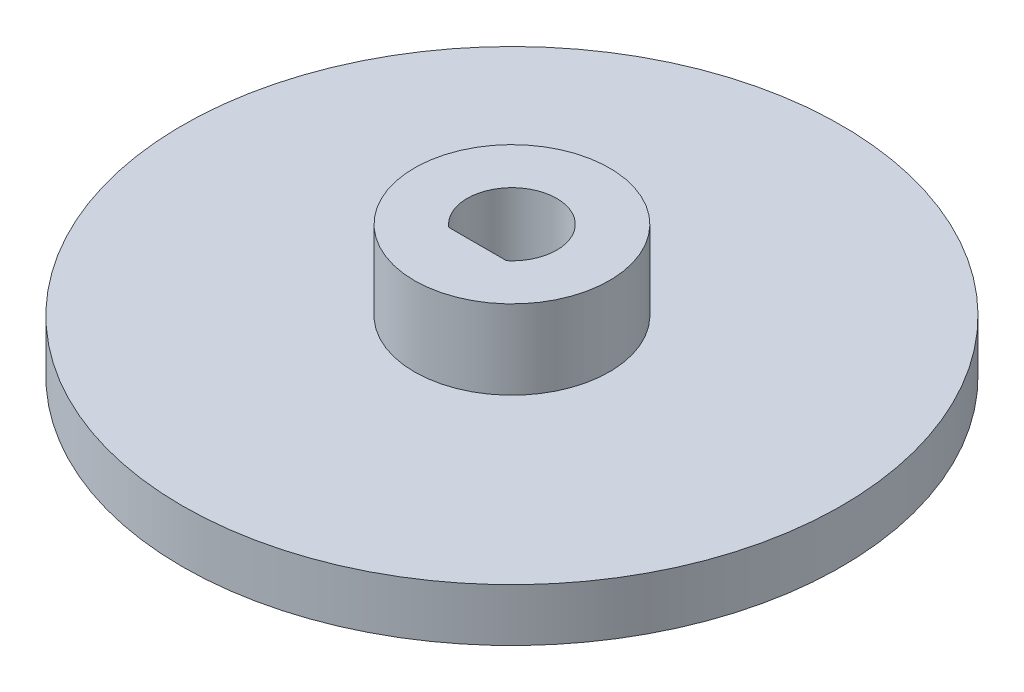
SolidWorks part; units mm, degrees
ref_plane "Front Plane" through (0, 0, 0) normal (0, 0, 1) x (1, 0, 0)
ref_plane "Top Plane" through (0, 0, 0) normal (0, 1, 0) x (1, 0, 0)
ref_plane "Right Plane" through (0, 0, 0) normal (1, 0, 0) x (0, 0, -1)
sketch "Sketch1" plane through (0, 0, 0) normal (0, 1, 0) x (1, 0, 0)
  line L0 (-1.0954, -1.3) -> (1.0954, -1.3)
  line L1 (0, -1.3) -> (0, -1.7)
  circle A0 centre (0, 0) radius 1.7
  circle A1 centre (0, 0) radius 12.5
  dimension "D1" = 3.4
  dimension "D2" = 25
  dimension "D3" = 0.4
extrude "Boss-Extrude1" add sketch "Sketch1" along normal blind 2 contours A1 A0 | L1 A0 L0 | L0 A0 L1
sketch "Sketch2" plane through (0, 2, 0) normal (0, 1, 0) x (1, 0, 0)
  line L1 (1.7, 0) -> (3.7, 0) construction
  line L2 (-1.0954, -1.3) -> (1.0954, -1.3)
  circle A0 centre (0, 0) radius 3.7
  arc A1 (1.0954, -1.3) -> (-1.0954, -1.3) centre (0, 0) ccw construction
  arc A2 (-1.0954, -1.3) -> (1.0954, -1.3) centre (0, 0) cw
  dimension "D2" = 1.7
  dimension "D1" = 2
extrude "Boss-Extrude2" add sketch "Sketch2" along normal blind 3
